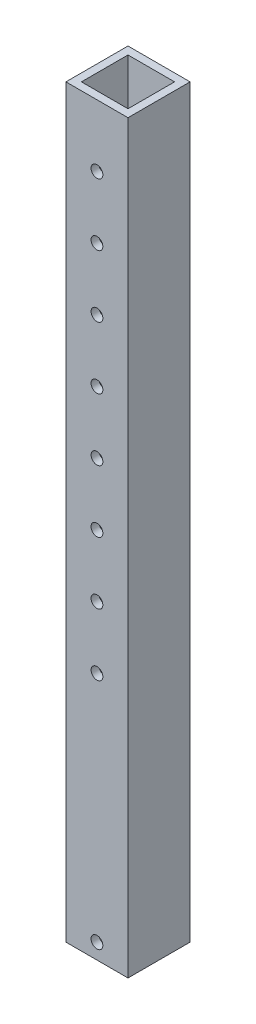
SolidWorks part; units mm, degrees
material "1060 Alloy"
ref_plane "Front Plane" through (0, 0, 0) normal (0, 0, 1) x (1, 0, 0)
ref_plane "Top Plane" through (0, 0, 0) normal (0, 1, 0) x (1, 0, 0)
ref_plane "Right Plane" through (0, 0, 0) normal (1, 0, 0) x (0, 0, -1)
sketch "Sketch2" plane through (0, 0, 0) normal (0, 1, 0) x (1, 0, 0)
  line L1 (-25.4, -25.4) -> (25.4, -25.4)
  line L2 (-25.4, -25.4) -> (-25.4, 25.4)
  line L3 (-25.4, 25.4) -> (25.4, 25.4)
  line L4 (25.4, -25.4) -> (25.4, 25.4)
  line L5 (-25.4, -25.4) -> (25.4, 25.4) construction
  line L6 (-25.4, 25.4) -> (25.4, -25.4) construction
  line L7 (-19.05, -19.05) -> (19.05, -19.05)
  line L8 (-19.05, -19.05) -> (-19.05, 19.05)
  line L9 (-19.05, 19.05) -> (19.05, 19.05)
  line L10 (19.05, -19.05) -> (19.05, 19.05)
  line L11 (-19.05, -19.05) -> (19.05, 19.05) construction
  line L12 (-19.05, 19.05) -> (19.05, -19.05) construction
  point P0 (0, 0)
  point P6 (0, 0)
  dimension "D1" = 50.8
  dimension "D2" = 50.8
  dimension "D3" = 38.1
  dimension "D4" = 38.1
extrude "Boss-Extrude1" add sketch "Sketch2" along normal blind 609.6
sketch "Sketch3" plane through (0, 0, 25.4) normal (0, 0, 1) x (1, 0, 0)
  line L0 (-25.4, 609.6) -> (25.4, 609.6) construction
  line L1 (-25.4, 609.6) -> (-25.4, 0) construction
  circle A0 centre (0, 12.7) radius 4.826
  circle A1 centre (0, 558.8) radius 4.826
  circle A3 centre (0, 508) radius 4.826
  circle A4 centre (0, 457.2) radius 4.826
  circle A5 centre (0, 406.4) radius 4.826
  circle A6 centre (0, 355.6) radius 4.826
  circle A7 centre (0, 304.8) radius 4.826
  circle A8 centre (0, 254) radius 4.826
  circle A9 centre (0, 203.2) radius 4.826
  dimension "D1" = 9.652
  dimension "D3" = 9.652
  dimension "D2" = 12.7
  dimension "D4" = 50.8
  dimension "D5" = 25.4
  dimension "D7" = 25.4
  dimension "D8" = 50.8
  dimension "D6" = 8
extrude "Cut-Extrude1" cut sketch "Sketch3" against normal blind 609.6 contours A1 | A3 | A4 | A5 | A6 | A7 | A8 | A9 | A0
